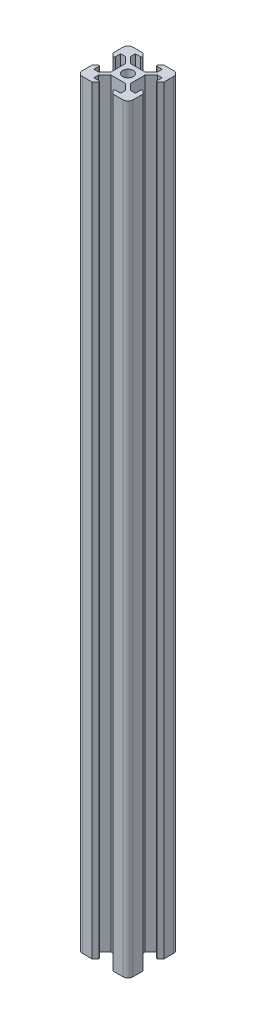
SolidWorks part; units mm, degrees
material "6063-T6"
ref_plane "Alzado" through (0, 0, 0) normal (0, 0, 1) x (1, 0, 0)
ref_plane "Planta" through (0, 0, 0) normal (0, 1, 0) x (1, 0, 0)
ref_plane "Vista lateral" through (0, 0, 0) normal (1, 0, 0) x (0, 0, -1)
sketch "Croquis1" plane through (0, 0, 0) normal (0, 1, 0) x (1, 0, 0)
  line L0 (0, 0) -> (-10, 10) construction
  line L1 (3.9, -2.84) -> (3.9, 2.84)
  line L2 (8.2, 5.3) -> (8.2, 3.34)
  line L3 (10, 8) -> (10, 4.14)
  line L4 (8.2, 5.3) -> (6.36, 5.3)
  line L5 (3.9, 2.84) -> (6.36, 5.3)
  line L6 (8.7, 2.84) -> (10, 4.14)
  line L7 (0, 0) -> (10, 10) construction
  line L8 (8, 10) -> (4.14, 10)
  line L9 (2.84, 8.7) -> (4.14, 10)
  line L10 (5.3, 8.2) -> (3.34, 8.2)
  line L11 (5.3, 8.2) -> (5.3, 6.36)
  line L12 (2.84, 3.9) -> (5.3, 6.36)
  line L13 (-2.84, 3.9) -> (2.84, 3.9)
  line L14 (-2.84, -3.9) -> (-5.3, -6.36)
  line L15 (-30.7915, 0) -> (30.7915, 0) construction
  line L16 (3.9, -2.84) -> (6.36, -5.3)
  line L17 (8.2, -5.3) -> (6.36, -5.3)
  line L18 (8.2, -5.3) -> (8.2, -3.34)
  line L19 (8.7, -2.84) -> (10, -4.14)
  line L20 (10, -8) -> (10, -4.14)
  line L21 (8, -10) -> (4.14, -10)
  line L22 (2.84, -8.7) -> (4.14, -10)
  line L23 (5.3, -8.2) -> (3.34, -8.2)
  line L24 (5.3, -8.2) -> (5.3, -6.36)
  line L25 (2.84, -3.9) -> (5.3, -6.36)
  line L26 (-2.84, -3.9) -> (2.84, -3.9)
  line L27 (0, 0) -> (0, 15.4885) construction
  line L28 (0, 0) -> (0, -17.6665) construction
  line L29 (0, 0) -> (-18.0561, 0) construction
  line L30 (-5.3, -8.2) -> (-5.3, -6.36)
  line L31 (-5.3, -8.2) -> (-3.34, -8.2)
  line L32 (-2.84, -8.7) -> (-4.14, -10)
  line L33 (-8, -10) -> (-4.14, -10)
  line L34 (-10, -8) -> (-10, -4.14)
  line L35 (-8.7, -2.84) -> (-10, -4.14)
  line L36 (-8.2, -5.3) -> (-8.2, -3.34)
  line L37 (-8.2, -5.3) -> (-6.36, -5.3)
  line L38 (-3.9, -2.84) -> (-6.36, -5.3)
  line L39 (-2.84, 3.9) -> (-5.3, 6.36)
  line L40 (-5.3, 8.2) -> (-5.3, 6.36)
  line L41 (-5.3, 8.2) -> (-3.34, 8.2)
  line L42 (-2.84, 8.7) -> (-4.14, 10)
  line L43 (-8, 10) -> (-4.14, 10)
  line L44 (-8.7, 2.84) -> (-10, 4.14)
  line L45 (-3.9, 2.84) -> (-6.36, 5.3)
  line L46 (-8.2, 5.3) -> (-6.36, 5.3)
  line L47 (-10, 8) -> (-10, 4.14)
  line L48 (-8.2, 5.3) -> (-8.2, 3.34)
  line L49 (-3.9, -2.84) -> (-3.9, 2.84)
  arc A0 (8.2, 3.34) -> (8.7, 2.84) centre (8.7, 3.34) ccw
  arc A1 (3.34, 8.2) -> (2.84, 8.7) centre (3.34, 8.7) cw
  arc A2 (10, 8) -> (8, 10) centre (8, 8) ccw
  arc A3 (8.2, -3.34) -> (8.7, -2.84) centre (8.7, -3.34) cw
  arc A4 (10, -8) -> (8, -10) centre (8, -8) cw
  arc A5 (3.34, -8.2) -> (2.84, -8.7) centre (3.34, -8.7) ccw
  arc A6 (-3.34, -8.2) -> (-2.84, -8.7) centre (-3.34, -8.7) cw
  arc A7 (-10, -8) -> (-8, -10) centre (-8, -8) ccw
  arc A8 (-8.2, -3.34) -> (-8.7, -2.84) centre (-8.7, -3.34) ccw
  arc A9 (-10, 8) -> (-8, 10) centre (-8, 8) cw
  arc A10 (-3.34, 8.2) -> (-2.84, 8.7) centre (-3.34, 8.7) ccw
  arc A11 (-8.2, 3.34) -> (-8.7, 2.84) centre (-8.7, 3.34) cw
  circle A12 centre (0, 0) radius 2.1
  point P11 (8.2, 2.84)
  point P65 (0, -3.9)
  point P73 (0, 3.9)
  point P80 (-8.2, 2.84)
  dimension "D9" = 0.5
  dimension "D12" = 2
  dimension "D13" = 4.2
  dimension "D2" = 3.9
  dimension "D3" = 3.9
  dimension "D4" = 2.46
  dimension "D5" = 5.86
  dimension "D6" = 1.96
  dimension "D7" = 0.7495
  dimension "D8" = 10
  dimension "D10" = 1.84
  dimension "D11" = 1.3
extrude "Saliente-Extruir2" add sketch "Croquis1" along normal blind 300
